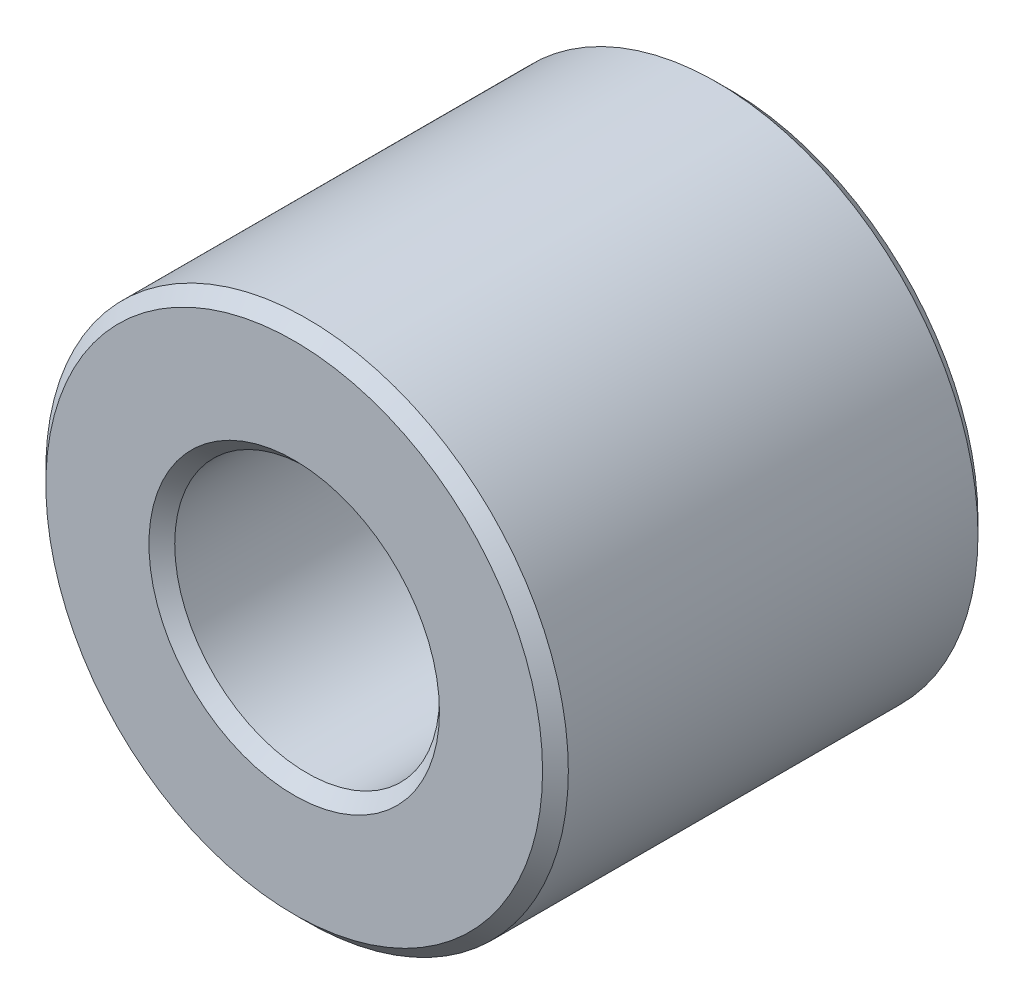
SolidWorks part; units mm, degrees
ref_plane "Front Plane" through (0, 0, 0) normal (0, 0, 1) x (1, 0, 0)
ref_plane "Top Plane" through (0, 0, 0) normal (0, 1, 0) x (1, 0, 0)
ref_plane "Right Plane" through (0, 0, 0) normal (1, 0, 0) x (0, 0, -1)
sketch "Sketch1" plane through (0, 0, 0) normal (0, 0, 1) x (1, 0, 0)
  circle A0 centre (0, 0) radius 9.525 construction
  circle A1 centre (0, 0) radius 4.826 construction
  point P4 (0, 9.525)
  dimension "ID" = 9.652
  dimension "OD" = 19.05
sketch "Sketch2" plane through (0, 0, 0) normal (1, 0, 0) x (0, 0, -1)
  line L0 (-7.9375, 9.525) -> (7.9375, 9.525) construction
  dimension "Length" = 15.875
sketch "Sketch3" plane through (0, 0, 0) normal (0, 0, 1) x (1, 0, 0)
  circle A0 centre (0, 0) radius 4.826 construction
  circle A1 centre (0, 0) radius 9.525 construction
  circle A2 centre (0, 0) radius 4.826
  circle A3 centre (0, 0) radius 9.525
extrude "Boss-Extrude1" add sketch "Sketch3" against normal up to vertex (7.9375 mm away) and the other way up to vertex (7.9375 mm away) up to point (0, 9.525, -7.9375) other way up to point (0, 9.525, 7.9375)
chamfer "Chamfer1" distance 0.4699 angle 45 4 edges at (9.525, 0, 7.9375) (9.525, 0, -7.9375) (4.826, 0, 7.9375) (4.826, 0, -7.9375)
equation "\"D1@Chamfer1\"=(\"OD@Sketch1\"-\"ID@Sketch1\")*0.05"
